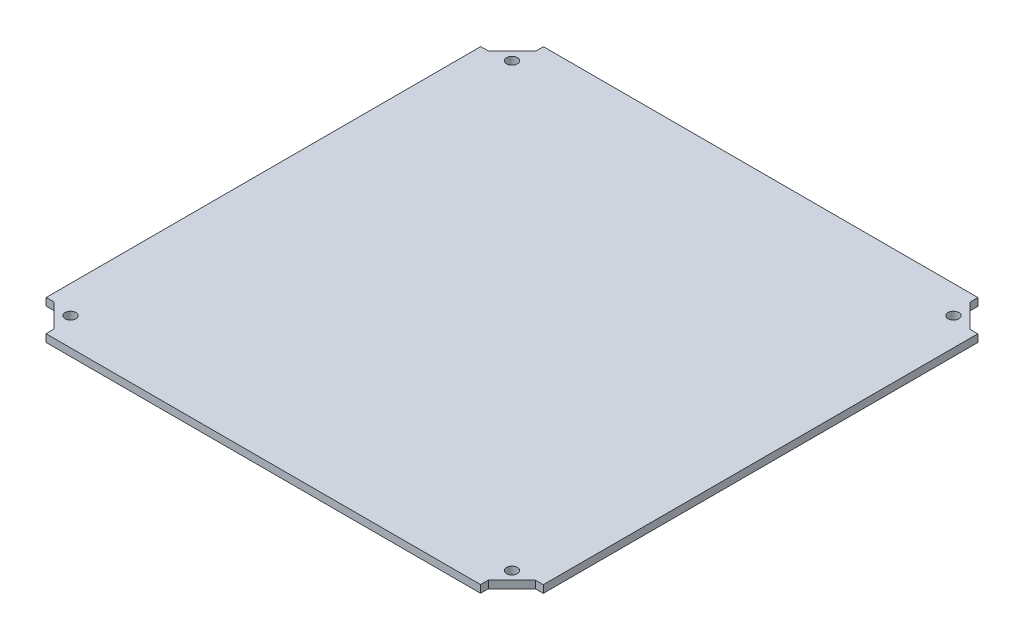
SolidWorks part; units mm, degrees
ref_plane "Front Plane" through (0, 0, 0) normal (0, 0, 1) x (1, 0, 0)
ref_plane "Top Plane" through (0, 0, 0) normal (0, 1, 0) x (1, 0, 0)
ref_plane "Right Plane" through (0, 0, 0) normal (1, 0, 0) x (0, 0, -1)
sketch "Sketch1" plane through (0, 0, 0) normal (0, 1, 0) x (1, 0, 0)
  line L0 (-91.2333, 104.4575) -> (-91.2333, 101.1555)
  line L1 (-91.3214, -104.4575) -> (91.2333, -104.4575)
  line L2 (-104.4575, -91.2333) -> (-104.4575, 91.3214)
  line L3 (-91.2333, 104.4575) -> (91.3214, 104.4575)
  line L4 (104.4575, -91.3214) -> (104.4575, 91.2333)
  line L5 (-117.475, -117.475) -> (117.475, 117.475) construction
  line L6 (-117.475, 117.475) -> (117.475, -117.475) construction
  line L7 (-101.1555, 91.3214) -> (-91.2333, 101.1555)
  line L8 (-104.4575, 91.3214) -> (-101.1555, 91.3214)
  line L9 (-104.4575, 91.3214) -> (-104.4575, 104.4575)
  line L10 (-104.4575, 104.4575) -> (-91.2333, 104.4575)
  line L11 (91.3214, 104.4575) -> (104.4575, 104.4575)
  line L12 (104.4575, 104.4575) -> (104.4575, 91.2333)
  line L13 (91.3214, 104.4575) -> (91.3214, 101.1555)
  line L14 (104.4575, 91.2333) -> (101.1555, 91.2333)
  line L15 (104.4575, -91.3214) -> (101.1555, -91.3214)
  line L16 (91.2333, -104.4575) -> (91.2333, -101.1555)
  line L17 (-91.3214, -104.4575) -> (-91.3214, -101.1555)
  line L18 (-104.4575, -91.2333) -> (-101.1555, -91.2333)
  line L19 (91.3214, 101.1555) -> (101.1555, 91.2333)
  line L20 (91.2333, -101.1555) -> (101.1555, -91.3214)
  line L21 (-101.1555, -91.2333) -> (-91.3214, -101.1555)
  line L22 (91.2333, -104.4575) -> (104.4575, -104.4575)
  line L23 (104.4575, -104.4575) -> (104.4575, -91.3214)
  line L24 (-104.4575, -91.2333) -> (-104.4575, -104.4575)
  line L25 (-104.4575, -104.4575) -> (-91.3214, -104.4575)
  point P0 (0, 0)
  dimension "D2" = 3.302
  dimension "D3" = 3.302
  dimension "D4" = 13.97
  dimension "D5" = 208.915
  dimension "D6" = 104.4575
  dimension "D7" = 13.97
  dimension "D8" = 104.4575
  dimension "D9" = 13.97
  dimension "D10" = 13.2242
  dimension "D11" = 13.97
  dimension "D12" = 208.915
extrude "Boss-Extrude1" add sketch "Sketch1" along normal blind 3.175
sketch "Sketch3" plane through (0, 3.175, 0) normal (0, 1, 0) x (1, 0, 0)
  line L0 (-92.7341, 92.7341) -> (92.7341, 92.7341)
  line L1 (92.7341, 92.7341) -> (92.7341, -92.7341)
  line L2 (92.7341, -92.7341) -> (-92.7341, -92.7341)
  line L3 (-92.7341, -92.7341) -> (-92.7341, 92.7341)
  line L19 (-91.3214, -104.4575) -> (91.2333, -104.4575)
  line L21 (-104.4575, -91.2333) -> (-101.1555, -91.2333)
  line L22 (-104.4575, -91.2333) -> (-101.1555, -91.2333)
  line L23 (104.4575, -91.3214) -> (104.4575, 91.2333)
  line L24 (-101.1555, -91.2333) -> (-91.3214, -101.1555)
  line L25 (-101.1555, -91.2333) -> (-91.3214, -101.1555)
  line L26 (-91.3214, -101.1555) -> (-91.3214, -104.4575)
  line L27 (91.3214, 104.4575) -> (-91.2333, 104.4575)
  line L28 (-91.3214, -101.1555) -> (-91.3214, -104.4575)
  line L29 (91.2333, -104.4575) -> (91.2333, -101.1555)
  line L30 (91.2333, -104.4575) -> (91.2333, -101.1555)
  line L31 (-104.4575, 91.3214) -> (-104.4575, -91.2333)
  line L35 (-91.3214, -104.4575) -> (91.2333, -104.4575)
  line L39 (104.4575, -91.3214) -> (104.4575, 91.2333)
  line L43 (91.3214, 104.4575) -> (-91.2333, 104.4575)
  line L47 (-104.4575, 91.3214) -> (-104.4575, -91.2333)
  line L48 (91.2333, -101.1555) -> (101.1555, -91.3214)
  line L49 (91.2333, -101.1555) -> (101.1555, -91.3214)
  line L50 (101.1555, -91.3214) -> (104.4575, -91.3214)
  line L51 (101.1555, -91.3214) -> (104.4575, -91.3214)
  line L52 (104.4575, 91.2333) -> (101.1555, 91.2333)
  line L53 (104.4575, 91.2333) -> (101.1555, 91.2333)
  line L54 (101.1555, 91.2333) -> (91.3214, 101.1555)
  line L55 (101.1555, 91.2333) -> (91.3214, 101.1555)
  line L56 (91.3214, 101.1555) -> (91.3214, 104.4575)
  line L57 (91.3214, 101.1555) -> (91.3214, 104.4575)
  line L58 (-91.2333, 104.4575) -> (-91.2333, 101.1555)
  line L59 (-91.2333, 104.4575) -> (-91.2333, 101.1555)
  line L60 (-91.2333, 101.1555) -> (-101.1555, 91.3214)
  line L61 (-91.2333, 101.1555) -> (-101.1555, 91.3214)
  line L62 (-101.1555, 91.3214) -> (-104.4575, 91.3214)
  line L63 (-101.1555, 91.3214) -> (-104.4575, 91.3214)
  circle A0 centre (-92.7341, 92.7341) radius 2.286
  circle A1 centre (92.7341, 92.7341) radius 2.286
  circle A2 centre (92.7341, -92.7341) radius 2.286
  circle A3 centre (-92.7341, -92.7341) radius 2.286
  point P7 (0, 0)
  point P13 (46.5305, 89.4025)
  point P18 (0, 92.7341)
  point P20 (-92.7341, 0)
  dimension "D2" = 4.572
  dimension "D3" = 185.4683
  dimension "D4" = 104.4575
  dimension "D5" = 104.4575
  dimension "D1" = 0
extrude "Cut-Extrude1" cut sketch "Sketch3" against normal up to next contours A0 | A1 | A2 | A3
sketch "Sketch4" plane through (0, 3.175, 0) normal (0, 1, 0) x (1, 0, 0)
  line L0 (-104.4575, 91.3214) -> (-104.4575, 104.4575)
  line L1 (-104.4575, 104.4575) -> (-91.2333, 104.4575)
  line L2 (91.3214, 104.4575) -> (104.4575, 104.4575)
  line L3 (104.4575, 104.4575) -> (104.4575, 91.2333)
  line L4 (91.2333, -104.4575) -> (104.4575, -104.4575)
  line L5 (104.4575, -104.4575) -> (104.4575, -91.3214)
  line L6 (-104.4575, -91.2333) -> (-104.4575, -104.4575)
  line L7 (-91.3214, -104.4575) -> (-104.4575, -104.4575)
  line L16 (-104.4575, -91.2333) -> (-101.1555, -91.2333)
  line L17 (-101.1555, -91.2333) -> (-91.3214, -101.1555)
  line L18 (-91.3214, -101.1555) -> (-91.3214, -104.4575)
  line L19 (-91.3214, -104.4575) -> (91.2333, -104.4575)
  line L20 (91.2333, -104.4575) -> (91.2333, -101.1555)
  line L21 (91.2333, -101.1555) -> (101.1555, -91.3214)
  line L22 (101.1555, -91.3214) -> (104.4575, -91.3214)
  line L23 (104.4575, -91.3214) -> (104.4575, 91.2333)
  line L24 (104.4575, 91.2333) -> (101.1555, 91.2333)
  line L25 (101.1555, 91.2333) -> (91.3214, 101.1555)
  line L26 (91.3214, 101.1555) -> (91.3214, 104.4575)
  line L27 (91.3214, 104.4575) -> (-91.2333, 104.4575)
  line L28 (-91.2333, 104.4575) -> (-91.2333, 101.1555)
  line L29 (-91.2333, 101.1555) -> (-101.1555, 91.3214)
  line L30 (-101.1555, 91.3214) -> (-104.4575, 91.3214)
  line L31 (-104.4575, 91.3214) -> (-104.4575, -91.2333)
  line L32 (-104.4575, -91.2333) -> (-101.1555, -91.2333)
  line L33 (-101.1555, -91.2333) -> (-91.3214, -101.1555)
  line L34 (-91.3214, -101.1555) -> (-91.3214, -104.4575)
  line L36 (91.2333, -104.4575) -> (91.2333, -101.1555)
  line L37 (91.2333, -101.1555) -> (101.1555, -91.3214)
  line L38 (101.1555, -91.3214) -> (104.4575, -91.3214)
  line L40 (104.4575, 91.2333) -> (101.1555, 91.2333)
  line L41 (101.1555, 91.2333) -> (91.3214, 101.1555)
  line L42 (91.3214, 101.1555) -> (91.3214, 104.4575)
  line L44 (-91.2333, 104.4575) -> (-91.2333, 101.1555)
  line L45 (-91.2333, 101.1555) -> (-101.1555, 91.3214)
  line L46 (-101.1555, 91.3214) -> (-104.4575, 91.3214)
  point P8 (0, 0)
  point P12 (0, 0)
  dimension "D1" = 0
